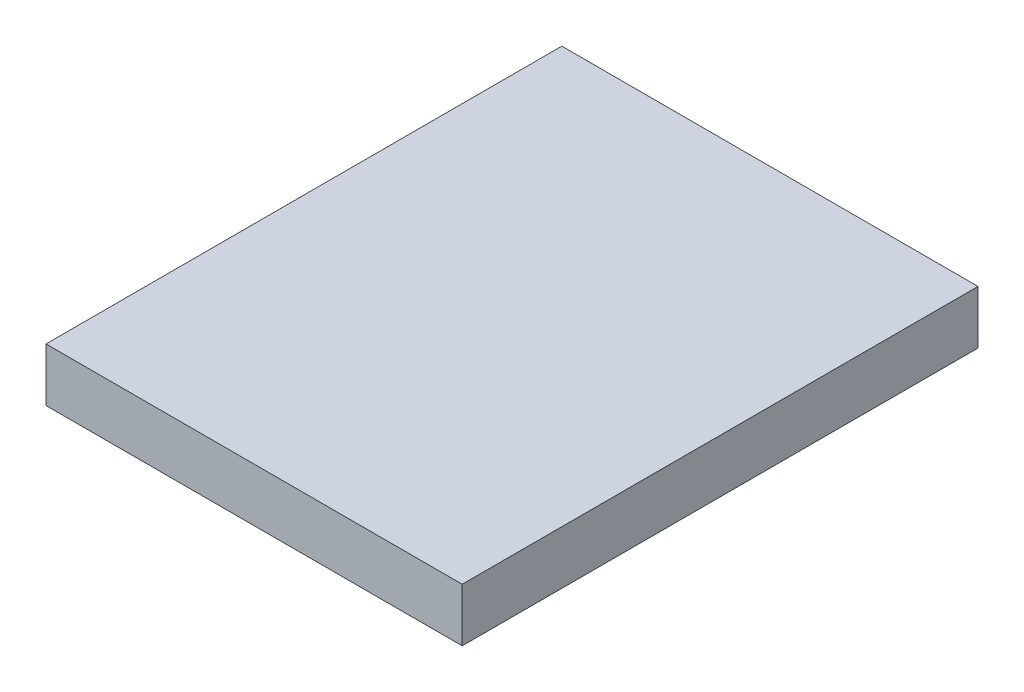
SolidWorks part; units mm, degrees
material "Custom Plastic"
ref_plane "Front Plane" through (0, 0, 0) normal (0, 0, 1) x (1, 0, 0)
ref_plane "Top Plane" through (0, 0, 0) normal (0, 1, 0) x (1, 0, 0)
ref_plane "Right Plane" through (0, 0, 0) normal (1, 0, 0) x (0, 0, -1)
sketch "Sketch1" plane through (0, 0, 0) normal (0, 1, 0) x (1, 0, 0)
  line L0 (-30.4611, 0) -> (33.997, 0) construction
  line L1 (-11.7, -14.5) -> (11.7, -14.5)
  line L2 (-11.7, -14.5) -> (-11.7, 14.5)
  line L3 (-11.7, 14.5) -> (11.7, 14.5)
  line L4 (11.7, -14.5) -> (11.7, 14.5)
  line L5 (-11.7, -14.5) -> (11.7, 14.5) construction
  line L6 (-11.7, 14.5) -> (11.7, -14.5) construction
  spline S1 degree 3 poles (19.181, -14.2425) (19.8008, -12.3411) (17.8993, -11.7212) (17.2795, -13.6227) (16.6596, -15.5241) (18.5612, -16.144) (19.181, -14.2425) (19.8008, -12.3411) (17.8993, -11.7212) knots -0.5 0 0 0 0.5 0.5 0.5 1 1 1 1.5 1.5 1.5 weights 1 0.333333 0.333333 1 0.333333 0.333333 1 0.333333 0.333333 only from (19.181, -14.2425) to (19.181, -14.2425) construction
  spline S2 degree 3 poles (22.4885, -4.0962) (23.1083, -2.1947) (21.2068, -1.5749) (20.587, -3.4763) (19.9671, -5.3778) (21.8687, -5.9977) (22.4885, -4.0962) (23.1083, -2.1947) (21.2068, -1.5749) knots -0.5 0 0 0 0.5 0.5 0.5 1 1 1 1.5 1.5 1.5 weights 1 0.333333 0.333333 1 0.333333 0.333333 1 0.333333 0.333333 only from (22.4885, -4.0962) to (22.4885, -4.0962) construction
  spline S3 degree 3 poles (19.181, -14.2425) (19.8008, -12.3411) (17.8993, -11.7212) (17.2795, -13.6227) (16.6596, -15.5241) (18.5612, -16.144) (19.181, -14.2425) (19.8008, -12.3411) (17.8993, -11.7212) knots -0.5 0 0 0 0.5 0.5 0.5 1 1 1 1.5 1.5 1.5 weights 1 0.333333 0.333333 1 0.333333 0.333333 1 0.333333 0.333333 only from (19.181, -14.2425) to (19.181, -14.2425)
  spline S4 degree 3 poles (22.4885, -4.0962) (23.1083, -2.1947) (21.2068, -1.5749) (20.587, -3.4763) (19.9671, -5.3778) (21.8687, -5.9977) (22.4885, -4.0962) (23.1083, -2.1947) (21.2068, -1.5749) knots -0.5 0 0 0 0.5 0.5 0.5 1 1 1 1.5 1.5 1.5 weights 1 0.333333 0.333333 1 0.333333 0.333333 1 0.333333 0.333333 only from (22.4885, -4.0962) to (22.4885, -4.0962)
  point P0 (0, 0)
  point P6 (-9, 8.5)
  point P7 (9, 8.5)
  point P8 (9, 8.9)
  point P18 (1.7, 8.5)
  dimension "D8" = 18
  dimension "D1" = 29
  dimension "D2" = 23.4
  dimension "D3" = 6
  dimension "D4" = 6
  dimension "D5" = 18
  dimension "D6" = 2.7
  dimension "D9" = 10.7
extrude "Boss-Extrude1" add sketch "Sketch1" along normal blind 3
sketch "Sketch5" plane through (0, 0, 0) normal (0, -1, 0) x (1, 0, 0)
  circle A0 centre (-2.1456, 3.6104) radius 2.5 construction
  circle A1 centre (-2.1456, 3.6104) radius 2.5 construction
  circle A2 centre (-2.1456, 3.6104) radius 1.44
  dimension "D1" = 2.88
extrude "Cut-Extrude3" cut sketch "Sketch5" against normal blind 10
sketch "Sketch7" plane through (0, 3, 0) normal (0, 1, 0) x (1, 0, 0)
  spline S0 degree 3 poles (19.181, -14.2425) (19.8008, -12.3411) (17.8993, -11.7212) (17.2795, -13.6227) (16.6596, -15.5241) (18.5612, -16.144) (19.181, -14.2425) (19.8008, -12.3411) (17.8993, -11.7212) knots -0.5 0 0 0 0.5 0.5 0.5 1 1 1 1.5 1.5 1.5 weights 1 0.333333 0.333333 1 0.333333 0.333333 1 0.333333 0.333333 only from (19.181, -14.2425) to (19.181, -14.2425) construction
  spline S1 degree 3 poles (22.4885, -4.0962) (23.1083, -2.1947) (21.2068, -1.5749) (20.587, -3.4763) (19.9671, -5.3778) (21.8687, -5.9977) (22.4885, -4.0962) (23.1083, -2.1947) (21.2068, -1.5749) knots -0.5 0 0 0 0.5 0.5 0.5 1 1 1 1.5 1.5 1.5 weights 1 0.333333 0.333333 1 0.333333 0.333333 1 0.333333 0.333333 only from (22.4885, -4.0962) to (22.4885, -4.0962) construction
  spline S2 degree 3 poles (19.181, -14.2425) (19.8008, -12.3411) (17.8993, -11.7212) (17.2795, -13.6227) (16.6596, -15.5241) (18.5612, -16.144) (19.181, -14.2425) (19.8008, -12.3411) (17.8993, -11.7212) knots -0.5 0 0 0 0.5 0.5 0.5 1 1 1 1.5 1.5 1.5 weights 1 0.333333 0.333333 1 0.333333 0.333333 1 0.333333 0.333333 only from (19.181, -14.2425) to (19.181, -14.2425)
  spline S3 degree 3 poles (22.4885, -4.0962) (23.1083, -2.1947) (21.2068, -1.5749) (20.587, -3.4763) (19.9671, -5.3778) (21.8687, -5.9977) (22.4885, -4.0962) (23.1083, -2.1947) (21.2068, -1.5749) knots -0.5 0 0 0 0.5 0.5 0.5 1 1 1 1.5 1.5 1.5 weights 1 0.333333 0.333333 1 0.333333 0.333333 1 0.333333 0.333333 only from (22.4885, -4.0962) to (22.4885, -4.0962)
extrude "Cut-Extrude4" cut sketch "Sketch7" against normal blind 10
sketch "Sketch9" plane through (0, 3, 0) normal (0, 1, 0) x (1, 0, 0)
  circle A0 centre (-2.1456, -3.6104) radius 3.027
extrude "Boss-Extrude3" add sketch "Sketch9" against normal up to surface (3 mm away) up to face at (-2.1456, 0, 2.1704)
